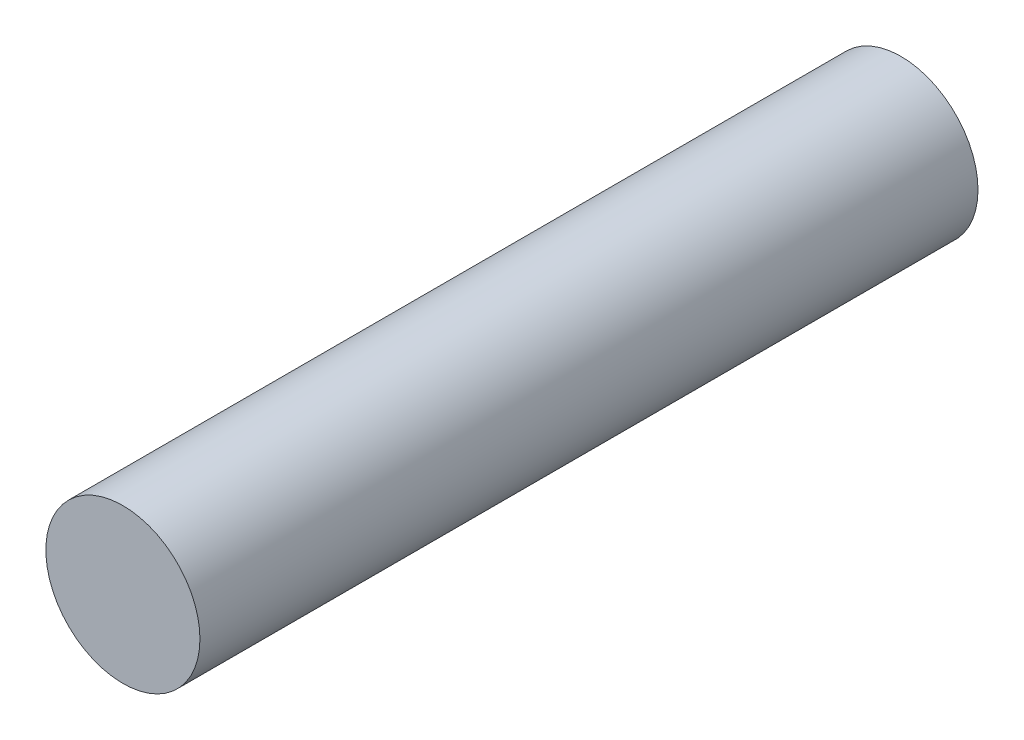
SolidWorks part; units mm, degrees
ref_plane "Front Plane" through (0, 0, 0) normal (0, 0, 1) x (1, 0, 0)
ref_plane "Top Plane" through (0, 0, 0) normal (0, 1, 0) x (1, 0, 0)
ref_plane "Right Plane" through (0, 0, 0) normal (1, 0, 0) x (0, 0, -1)
sketch "Sketch1" plane through (0, 0, 0) normal (0, 0, 1) x (1, 0, 0)
  circle A0 centre (0, 0) radius 2.54
  dimension "D1" = 5.08
extrude "Boss-Extrude1" add sketch "Sketch1" along normal blind 25.65
